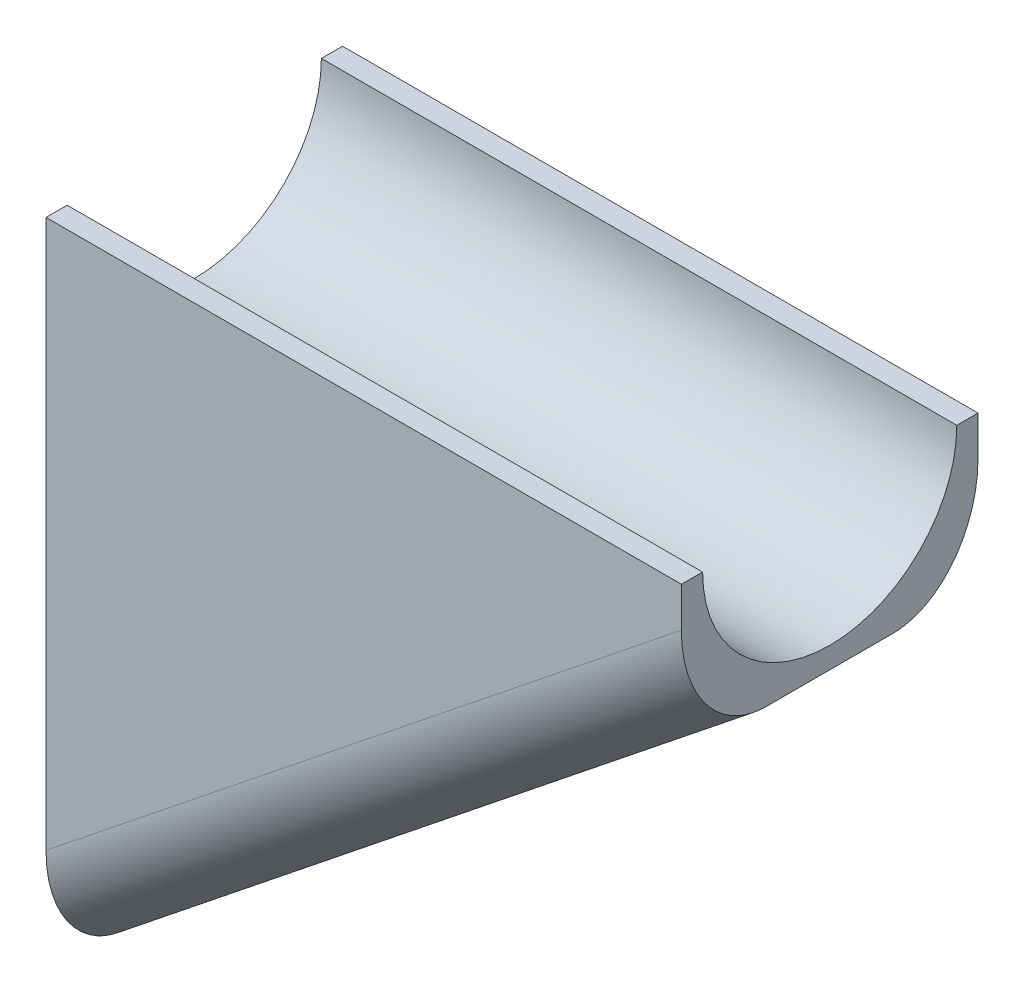
SolidWorks part; units mm, degrees
ref_plane "Front Plane" through (0, 0, 0) normal (0, 0, 1) x (1, 0, 0)
ref_plane "Top Plane" through (0, 0, 0) normal (0, 1, 0) x (1, 0, 0)
ref_plane "Right Plane" through (0, 0, 0) normal (1, 0, 0) x (0, 0, -1)
sketch "Sketch1" plane through (0, 0, 0) normal (0, 0, 1) x (1, 0, 0)
  line L0 (-7.5, -6) -> (7.5, 6)
  line L1 (7.5, -6) -> (-7.5, -6) construction
  line L2 (7.5, -6) -> (7.5, 6) construction
  line L3 (7.5, 6) -> (-7.5, 6) construction
  line L4 (-7.5, -6) -> (-7.5, 6) construction
  line L5 (-7.5, 6) -> (7.5, -6) construction
  line L6 (7.5, 6) -> (-7.5, -6) construction
  line L7 (7.5, 6) -> (-7.5, 6)
  line L8 (-7.5, 6) -> (-7.5, -6)
  line L14 (7.5, 6) -> (-7.5, -6) construction
  point P0 (0, 0)
  point P7 (0, 0)
  point P8 (0, 0)
  point P9 (0, 0)
  point P11 (5.3817, -1.2004)
  dimension "D1" = 12
  dimension "D2" = 15
extrude "Boss-Extrude1" add sketch "Sketch1" along normal blind 7
sketch "Sketch2" plane through (-7.5, 0, 0) normal (-1, 0, 0) x (0, 0, 1)
  line L1 (7, 6) -> (0, 6) construction
  point P7 (3.25, 6)
sketch "Sketch3" plane through (0, 6, 0) normal (0, 1, 0) x (1, 0, 0)
  line L1 (-7.5, 0) -> (7.5, 0)
  line L2 (-7.5, 0) -> (-7.5, -7)
  line L3 (-7.5, -7) -> (7.5, -7)
  line L4 (7.5, 0) -> (7.5, -7)
extrude "Boss-Extrude2" add sketch "Sketch3" along normal blind 3.5
sketch "Sketch4" plane through (7.5, 0, 0) normal (1, 0, 0) x (0, 0, -1)
  line L0 (-7, 9.5) -> (0, 9.5) construction
  arc A0 (-6.5, 9.5) -> (-0.5, 9.5) centre (-3.5, 9.5) ccw
  point P0 (-3.5, 9.5)
  point P6 (-3.25, 8.5557)
  point P7 (-1.7927, 9)
  point P8 (-3.25, 8.8289)
  point P9 (0, 0)
  dimension "D1" = 3
extrude "Cut-Extrude1" cut sketch "Sketch4" against normal through all and the other way through all
fillet "Fillet1" radius 2 2 edges at (0, 0, 0) (0, 0, 7)
